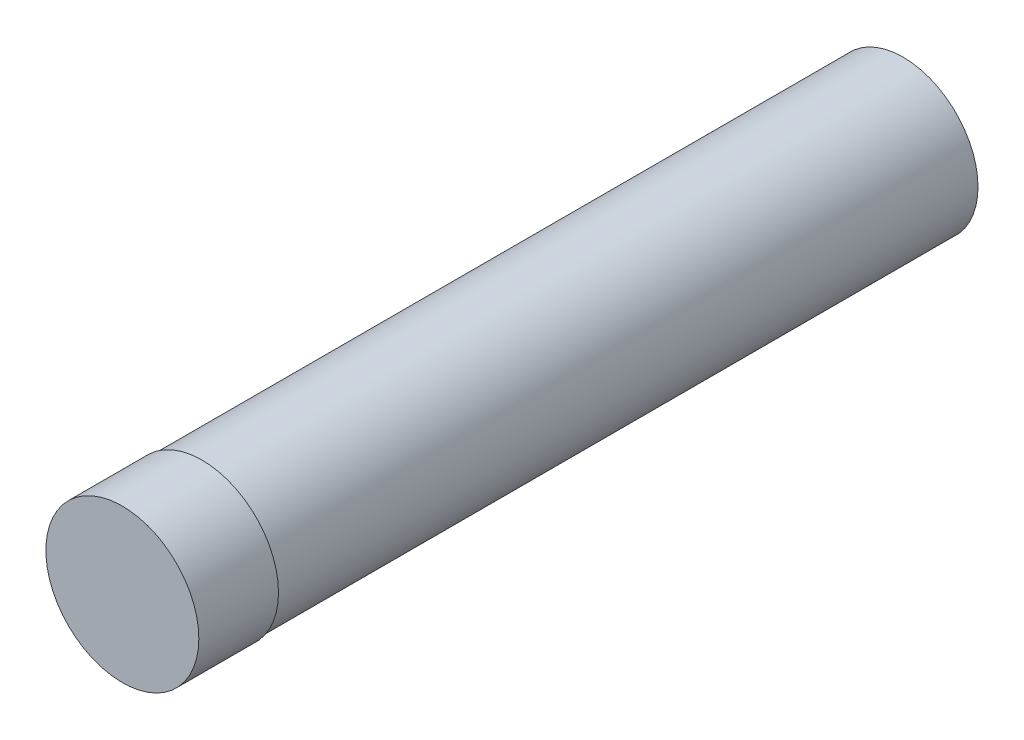
SolidWorks part; units mm, degrees
ref_plane "Front Plane" through (0, 0, 0) normal (0, 0, 1) x (1, 0, 0)
ref_plane "Top Plane" through (0, 0, 0) normal (0, 1, 0) x (1, 0, 0)
ref_plane "Right Plane" through (0, 0, 0) normal (1, 0, 0) x (0, 0, -1)
sketch "Sketch1" plane through (0, 0, 0) normal (0, 0, 1) x (1, 0, 0)
  circle A0 centre (0, 0) radius 4.8
  dimension "D1" = 9.6
extrude "Boss-Extrude1" add sketch "Sketch1" along normal blind 5
sketch "Sketch2" plane through (0, 0, 0) normal (0, 0, -1) x (-1, 0, 0)
  circle A0 centre (0, 0) radius 3.7
  dimension "D1" = 7.4
extrude "Extrude-Thin3" add sketch "Sketch2" along normal blind 44 thin contours A0
